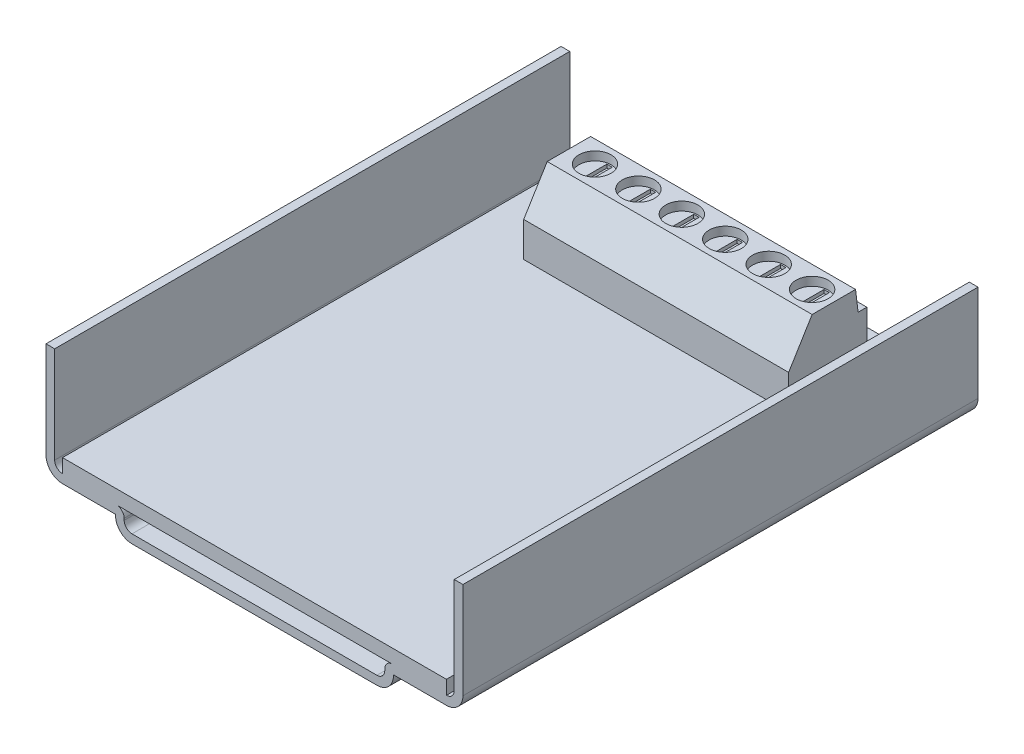
SolidWorks part; units mm, degrees
ref_plane "Front Plane" through (0, 0, 0) normal (0, 0, 1) x (1, 0, 0)
ref_plane "Top Plane" through (0, 0, 0) normal (0, 1, 0) x (1, 0, 0)
ref_plane "Right Plane" through (0, 0, 0) normal (1, 0, 0) x (0, 0, -1)
sketch "Sketch1" plane through (0, 0, 0) normal (0, 0, 1) x (1, 0, 0)
  line L0 (-28.3239, 14) -> (-28.3239, 2.9)
  line L1 (-27.4239, 2) -> (-21.2239, 2)
  line L2 (-20.3239, 1.1) -> (-20.3239, 0.9)
  line L3 (-19.4239, 0) -> (8.7761, 0)
  line L4 (9.6761, 0.9) -> (9.6761, 1.1)
  line L5 (10.5761, 2) -> (16.7761, 2)
  line L6 (17.6761, 2.9) -> (17.6761, 14)
  arc A0 (-28.3239, 2.9) -> (-27.4239, 2) centre (-27.4239, 2.9) ccw
  arc A1 (-21.2239, 2) -> (-20.3239, 1.1) centre (-21.2239, 1.1) cw
  arc A2 (16.7761, 2) -> (17.6761, 2.9) centre (16.7761, 2.9) ccw
  arc A3 (9.6761, 1.1) -> (10.5761, 2) centre (10.5761, 1.1) cw
  arc A4 (8.7761, 0) -> (9.6761, 0.9) centre (8.7761, 0.9) ccw
  arc A5 (-20.3239, 0.9) -> (-19.4239, 0) centre (-19.4239, 0.9) ccw
  point P11 (-28.3239, 2)
  point P14 (-20.3239, 2)
  point P17 (17.6761, 2)
  point P20 (9.6761, 2)
  point P23 (9.6761, 0)
  point P26 (-20.3239, 0)
  dimension "D8" = 0.9
  dimension "D9" = 0.9
  dimension "D10" = 0.9
  dimension "D1" = 12
  dimension "D2" = 8
  dimension "D3" = 12
  dimension "D4" = 8
  dimension "D5" = 46
  dimension "D6" = 2
  dimension "D7" = 2
extrude "Extrude-Thin1" add sketch "Sketch1" against normal blind 59.3 thin
sketch "Sketch2" plane through (0, 2, 0) normal (0, 1, 0) x (1, 0, 0)
  line L1 (-27.4239, 59.3) -> (16.7761, 59.3)
  line L2 (-27.4239, 59.3) -> (-27.4239, 0)
  line L3 (-27.4239, 0) -> (16.7761, 0)
  line L4 (16.7761, 59.3) -> (16.7761, 0)
extrude "Extrude1" add sketch "Sketch2" along normal blind 1.6 separate body
ref_plane "Plane1" through (9.8761, 0, 0) normal (-1, 0, 0) x (0, 0, 1)
sketch "Sketch3" plane through (9.8761, 0, 0) normal (-1, 0, 0) x (0, 0, 1)
  line L0 (-55.3, 3.6) -> (-46.3, 3.6)
  line L1 (-59.3, 3.6) -> (0, 3.6) construction
  line L2 (-46.3, 3.6) -> (-46.3, 7.6)
  line L3 (-46.3, 7.6) -> (-49.0031, 12.0201)
  line L4 (-49.0031, 12.0201) -> (-54.0031, 12.0201)
  line L5 (-54.0031, 12.0201) -> (-54.3, 9.6)
  line L6 (-54.3, 9.6) -> (-55.3, 9.6)
  line L7 (-55.3, 9.6) -> (-55.3, 3.6)
  line L8 (-59.3, 14) -> (-59.3, 2.9) construction
  dimension "D1" = 9
  dimension "D2" = 6
  dimension "D3" = 1
  dimension "D4" = 4
  dimension "D5" = 5
  dimension "D6" = 4
extrude "Extrude2" add sketch "Sketch3" along normal blind 30.5
sketch "Sketch4" plane through (0, 12.0201, 0) normal (0, 1, 0) x (1, 0, 0)
  line L0 (-20.6239, 55.3) -> (-20.6239, 46.3) construction
  line L1 (-20.6239, 49.0031) -> (-20.6239, 54.0031) construction
  circle A0 centre (-17.6239, 51.5031) radius 1.85
  point P6 (-20.6239, 51.5031)
  dimension "D1" = 3.7
  dimension "D2" = 3
extrude "Extrude3" cut sketch "Sketch4" against normal blind 1.5
sketch "Sketch6" plane through (0, 10.5201, 0) normal (0, 1, 0) x (1, 0, 0)
  circle A0 centre (-17.6239, 51.5031) radius 1.85
extrude "Extrude4" add sketch "Sketch6" along normal blind 0.5
sketch "Sketch8" plane through (0, 11.0201, 0) normal (0, 1, 0) x (1, 0, 0)
  line L1 (-17.9314, 49.8285) -> (-17.3163, 49.8285)
  line L2 (-17.9314, 49.8285) -> (-17.9314, 53.1778)
  line L3 (-17.9314, 53.1778) -> (-17.3163, 53.1778)
  line L4 (-17.3163, 49.8285) -> (-17.3163, 53.1778)
  line L5 (-17.9314, 49.8285) -> (-17.3163, 53.1778) construction
  line L6 (-17.9314, 53.1778) -> (-17.3163, 49.8285) construction
  point P0 (-17.6239, 51.5031)
extrude "Extrude5" cut sketch "Sketch8" against normal blind 0.4
pattern_linear "LPattern1" count 6 spacing 5 along (1, 0, 0) of "Extrude5", "Extrude4", "Extrude3"
